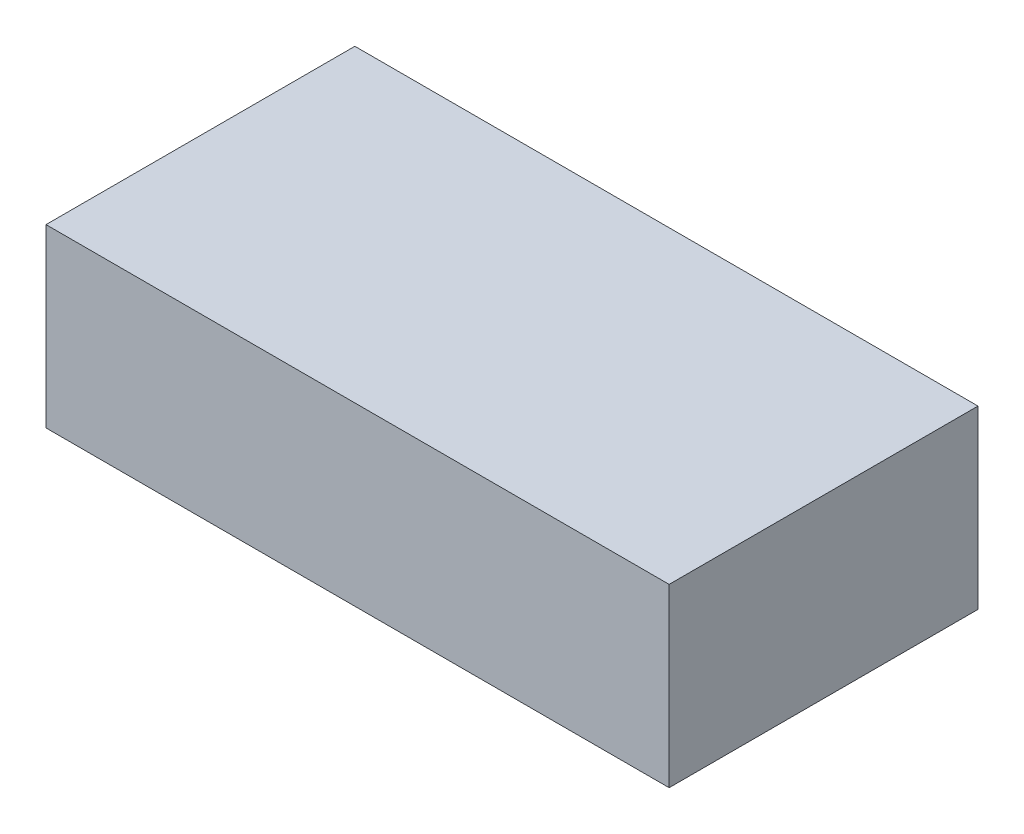
SolidWorks part; units mm, degrees
ref_plane "Спереди" through (0, 0, 0) normal (0, 0, 1) x (1, 0, 0)
ref_plane "Сверху" through (0, 0, 0) normal (0, 1, 0) x (1, 0, 0)
ref_plane "Справа" through (0, 0, 0) normal (1, 0, 0) x (0, 0, -1)
sketch "Эскиз1" plane through (0, 0, 0) normal (0, 1, 0) x (1, 0, 0)
  line L1 (0, 0) -> (230, 0)
  line L2 (0, 0) -> (0, 114)
  line L3 (0, 114) -> (230, 114)
  line L4 (230, 0) -> (230, 114)
extrude "Бобышка-Вытянуть1" add sketch "Эскиз1" along normal blind 65
